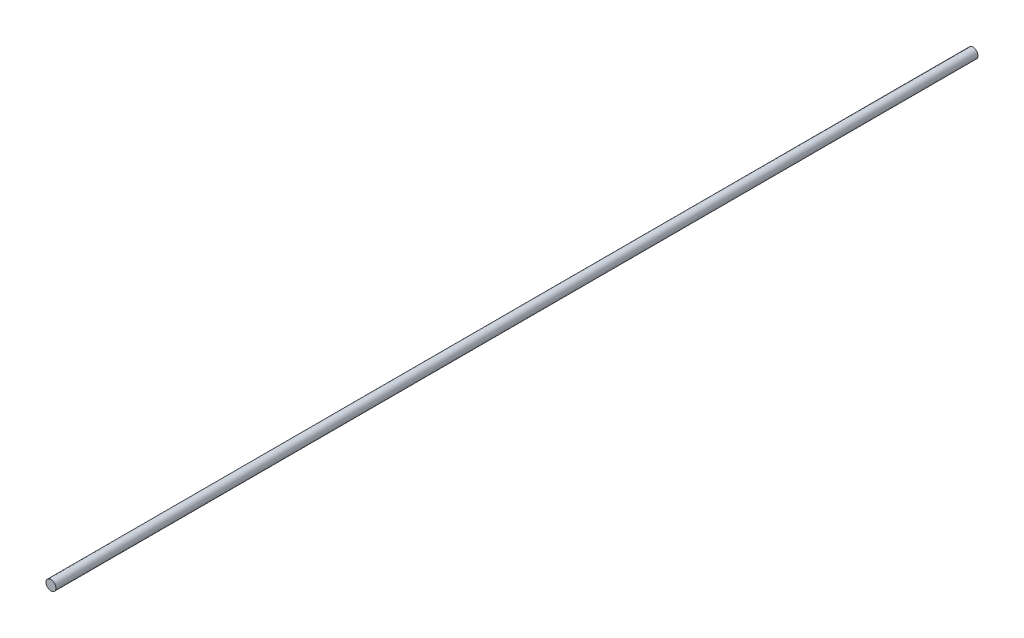
SolidWorks part; units mm, degrees
material "Alloy Steel"
ref_plane "Front Plane" through (0, 0, 0) normal (0, 0, 1) x (1, 0, 0)
ref_plane "Top Plane" through (0, 0, 0) normal (0, 1, 0) x (1, 0, 0)
ref_plane "Right Plane" through (0, 0, 0) normal (1, 0, 0) x (0, 0, -1)
sketch "Sketch1" plane through (0, 0, 0) normal (0, 0, 1) x (1, 0, 0)
  circle A0 centre (0, 0) radius 27.5
  dimension "D1" = 55
extrude "Boss-Extrude1" add sketch "Sketch1" along normal blind 5100
scale "Scale1" bodies to scale 101 scale about centroid uniform scaling yes scale factor 0.1
